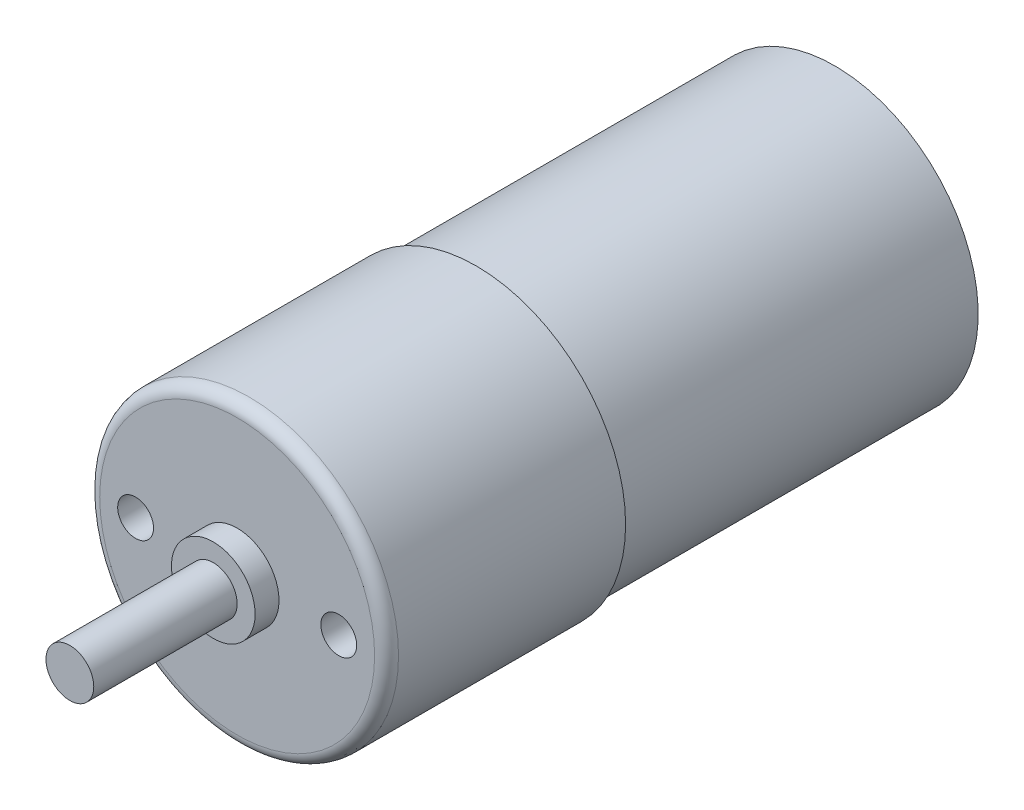
SolidWorks part; units mm, degrees
ref_plane "Front Plane" through (0, 0, 0) normal (0, 0, 1) x (1, 0, 0)
ref_plane "Top Plane" through (0, 0, 0) normal (0, 1, 0) x (1, 0, 0)
ref_plane "Right Plane" through (0, 0, 0) normal (1, 0, 0) x (0, 0, -1)
sketch "Sketch1" plane through (0, 0, 0) normal (0, 0, 1) x (1, 0, 0)
  circle A0 centre (0, 0) radius 12.5
  dimension "D1" = 25
extrude "Boss-Extrude1" add sketch "Sketch1" along normal blind 50
sketch "Sketch2" plane through (0, 0, 50) normal (0, 0, 1) x (1, 0, 0)
  circle A0 centre (0, 0) radius 3.5
  dimension "D1" = 7
extrude "Boss-Extrude2" add sketch "Sketch2" along normal blind 2
sketch "Sketch3" plane through (0, 0, 52) normal (0, 0, 1) x (1, 0, 0)
  circle A0 centre (0, 0) radius 2
  dimension "D1" = 4
extrude "Boss-Extrude3" add sketch "Sketch3" along normal blind 12
sketch "Sketch4" plane through (0, 0, 0) normal (0, 0, -1) x (-1, 0, 0)
  circle A0 centre (0, 0) radius 12
  circle A1 centre (0, 0) radius 12.5
  circle A2 centre (0, 0) radius 12.5
  dimension "D1" = 0
  dimension "D2" = 0.5
extrude "Cut-Extrude1" cut sketch "Sketch4" against normal blind 30
fillet "Fillet1" radius 1 1 edges at (12.5, 0, 50)
sketch "Sketch5" plane through (0, 0, 0) normal (0, 0, -1) x (-1, 0, 0)
  circle A0 centre (0, 0) radius 3.0708
extrude "Boss-Extrude4" add sketch "Sketch5" along normal blind 1
fillet "Fillet2" radius 0.5 1 edges at (-3.0708, 0, -1)
sketch "Sketch6" plane through (0, 0, 50) normal (0, 0, 1) x (1, 0, 0)
  line L0 (0, 0) -> (8.5, 0) construction
  line L1 (0, -13.75) -> (0, 13.75) construction
  circle A0 centre (8.5, 0) radius 1.5
  circle A1 centre (-8.5, 0) radius 1.5
  dimension "D2" = 3
  dimension "D1" = 8.5
extrude "Cut-Extrude2" cut sketch "Sketch6" against normal blind 10
